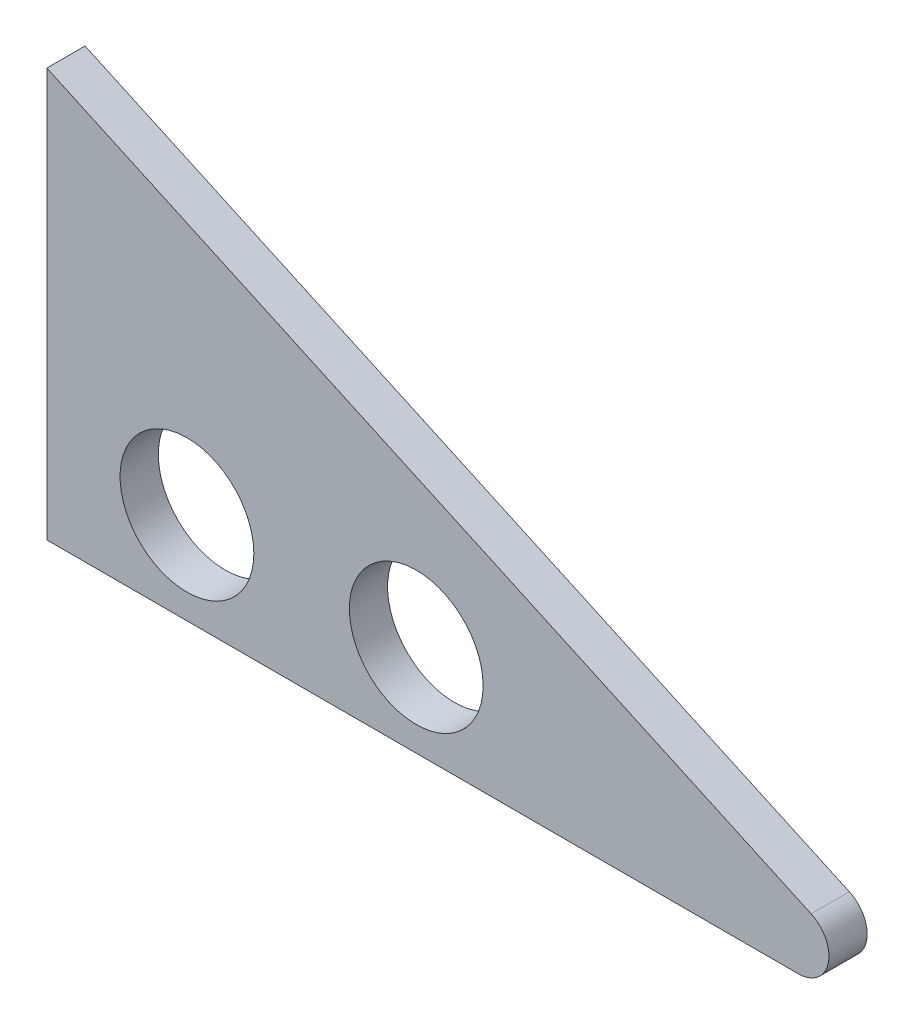
SolidWorks part; units mm, degrees
ref_plane "Front Plane" through (0, 0, 0) normal (0, 0, 1) x (1, 0, 0)
ref_plane "Top Plane" through (0, 0, 0) normal (0, 1, 0) x (1, 0, 0)
ref_plane "Right Plane" through (0, 0, 0) normal (1, 0, 0) x (0, 0, -1)
sketch "Sketch1" plane through (0, 0, 0) normal (0, 0, 1) x (1, 0, 0)
  line L1 (90.184, 0) -> (152.6257, 0)
  line L2 (153.684, 4.849) -> (90.184, 33.9542)
  line L3 (120.8757, 7.62) -> (76.3516, 7.62) construction
  line L4 (90.184, 0) -> (90.184, 33.9542)
  arc A2 (152.6257, 0) -> (153.684, 4.849) centre (152.6257, 2.54) ccw
  circle A3 centre (120.8757, 7.62) radius 5.5562
  circle A4 centre (101.8257, 7.62) radius 5.5563
  point P12 (164.2633, 0)
  dimension "D6" = 11.1125
  dimension "D2" = 11.6376
  dimension "D7" = 7.62
  dimension "D8" = 19.05
  dimension "D10" = 63.5
extrude "Extrude1" add sketch "Sketch1" along normal blind 3.175
